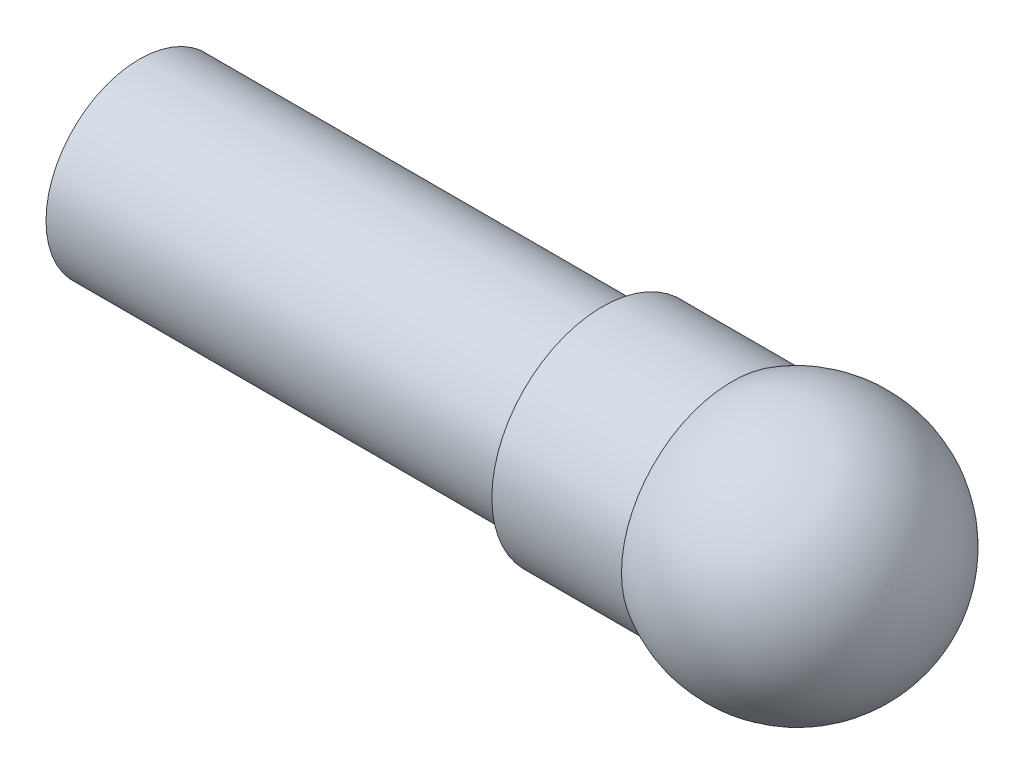
SolidWorks part; units mm, degrees
ref_plane "Front Plane" through (0, 0, 0) normal (0, 0, 1) x (1, 0, 0)
ref_plane "Top Plane" through (0, 0, 0) normal (0, 1, 0) x (1, 0, 0)
ref_plane "Right Plane" through (0, 0, 0) normal (1, 0, 0) x (0, 0, -1)
sketch "Sketch1" plane through (0, 0, 0) normal (0, 1, 0) x (1, 0, 0)
  line L0 (0, -2) -> (-14, -2)
  line L4 (0, -24) -> (-14, -24)
  line L5 (0, 0) -> (-14, 0)
  line L6 (0, -22.16) -> (-14, -22.16)
  line L7 (-64, -2) -> (-64, -4.3261)
  line L8 (-14, -2) -> (-64, -2)
  line L9 (-14, -4.3261) -> (-64, -4.3261)
  line L10 (-14, -20.16) -> (-64, -20.16)
  line L11 (-14, -4.3261) -> (0, -4.3261)
  line L12 (0, -4.3261) -> (0, -2)
  line L13 (-14, -20.16) -> (0, -20.16)
  line L14 (0, -20.16) -> (0, -22.16)
  line L15 (-14, -22.16) -> (-64, -22.16)
  line L16 (-64, -22.16) -> (-64, -20.16)
  line L17 (-14, 0) -> (-14, -2)
  line L18 (-14, -22.16) -> (-14, -24)
  line L19 (-74.4189, -12.08) -> (37.3623, -12.08)
  arc A3 (0, 0) -> (0, -24) centre (7.0159, -12) cw
  arc A4 (0, -2) -> (0, -22.16) centre (6.7523, -12.08) cw
  dimension "D1" = 50
  dimension "D2" = 50
revolve "Revolve3" add sketch "Sketch1" angle 360 about L19
